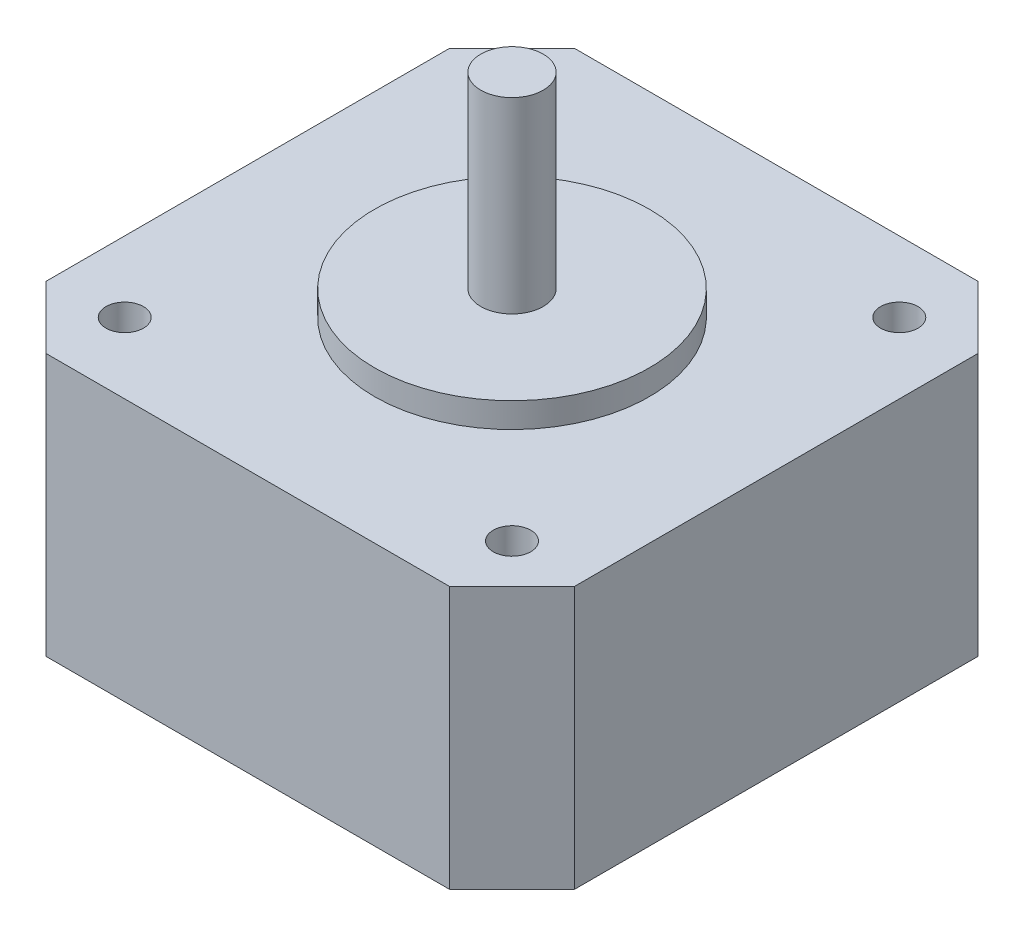
SolidWorks part; units mm, degrees
ref_plane "Front Plane" through (0, 0, 0) normal (0, 0, 1) x (1, 0, 0)
ref_plane "Top Plane" through (0, 0, 0) normal (0, 1, 0) x (1, 0, 0)
ref_plane "Right Plane" through (0, 0, 0) normal (1, 0, 0) x (0, 0, -1)
sketch "Sketch1" plane through (0, 0, 0) normal (0, 1, 0) x (1, 0, 0)
  line L1 (-21.15, 21.15) -> (21.15, 21.15)
  line L2 (-21.15, 21.15) -> (-21.15, -21.15)
  line L3 (-21.15, -21.15) -> (21.15, -21.15)
  line L4 (21.15, 21.15) -> (21.15, -21.15)
  line L5 (-21.15, 21.15) -> (21.15, -21.15) construction
  line L6 (-21.15, -21.15) -> (21.15, 21.15) construction
  point P0 (0, 0)
  dimension "D1" = 42.3
  dimension "D2" = 42.3
extrude "Boss-Extrude1" add sketch "Sketch1" along normal blind 21
chamfer "Chamfer1" distance 5 angle 45 4 edges at (-21.15, 10.5, 21.15) (-21.15, 10.5, -21.15) (21.15, 10.5, -21.15) (21.15, 10.5, 21.15)
sketch "Sketch2" plane through (0, 21, 0) normal (0, 1, 0) x (1, 0, 0)
  line L1 (-15.5, 15.5) -> (15.5, 15.5) construction
  line L2 (-15.5, 15.5) -> (-15.5, -15.5) construction
  line L3 (-15.5, -15.5) -> (15.5, -15.5) construction
  line L4 (15.5, 15.5) -> (15.5, -15.5) construction
  line L5 (-15.5, 15.5) -> (15.5, -15.5) construction
  line L6 (-15.5, -15.5) -> (15.5, 15.5) construction
  circle A0 centre (15.5, -15.5) radius 1.5
  circle A1 centre (15.5, 15.5) radius 1.5
  circle A2 centre (-15.5, 15.5) radius 1.5
  circle A3 centre (-15.5, -15.5) radius 1.5
  point P0 (0, 0)
  dimension "D2" = 3
  dimension "D1" = 31
extrude "Cut-Extrude1" cut sketch "Sketch2" against normal blind 3
sketch "Sketch3" plane through (0, 21, 0) normal (0, 1, 0) x (1, 0, 0)
  circle A0 centre (0, 0) radius 11
  dimension "D1" = 22
extrude "Boss-Extrude2" add sketch "Sketch3" along normal blind 2
sketch "Sketch4" plane through (0, 23, 0) normal (0, 1, 0) x (1, 0, 0)
  circle A0 centre (0, 0) radius 2.5
  dimension "D1" = 5
extrude "Boss-Extrude3" add sketch "Sketch4" along normal blind 15
